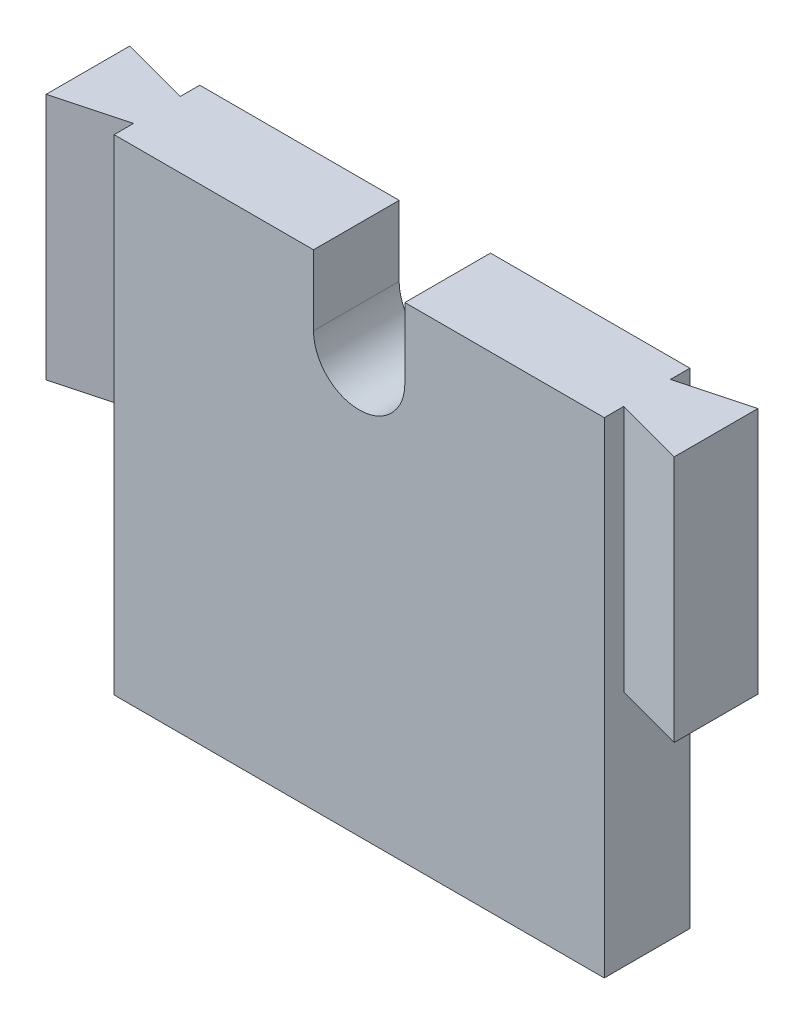
SolidWorks part; units mm, degrees
ref_plane "Front Plane" through (0, 0, 0) normal (0, 0, 1) x (1, 0, 0)
ref_plane "Top Plane" through (0, 0, 0) normal (0, 1, 0) x (1, 0, 0)
ref_plane "Right Plane" through (0, 0, 0) normal (1, 0, 0) x (0, 0, -1)
sketch "Sketch2" plane through (0, 0, 0) normal (0, 0, 1) x (1, 0, 0)
  line L0 (-10.1529, 26.4118) -> (-0.5529, 26.4118)
  line L1 (-38.3529, 26.4118) -> (27.6471, 26.4118)
  line L2 (-38.3529, 26.4118) -> (-38.3529, -24.5882)
  line L3 (-38.3529, -24.5882) -> (27.6471, -24.5882)
  line L4 (27.6471, 26.4118) -> (27.6471, -24.5882)
  line L5 (-5.3529, 26.4118) -> (-5.3529, -24.5882) construction
  line L6 (-10.1529, 19.0368) -> (-10.1529, 26.4118)
  line L7 (-0.5529, 19.0368) -> (-0.5529, 26.4118)
  arc A0 (-10.1529, 19.0368) -> (-0.5529, 19.0368) centre (-5.3529, 19.0368) ccw
  dimension "D4" = 9.6
  dimension "D1" = 66
  dimension "D2" = 51
extrude "Boss-Extrude1" add sketch "Sketch2" along normal blind 9
sketch "Sketch3" plane through (0, 26.4118, 0) normal (0, 1, 0) x (1, 0, 0)
  line L0 (28.0533, 0) -> (20.4026, -2.05)
  line L1 (20.4026, -2.05) -> (20.4026, 0)
  line L2 (-0.5529, 0) -> (27.6471, 0) construction
  line L3 (28.0533, -9) -> (20.4026, -6.95)
  line L4 (20.4026, -6.95) -> (20.4026, -9)
  line L5 (-0.5529, -9) -> (27.6471, -9) construction
  line L6 (27.6471, -9) -> (27.6471, 0) construction
  line L7 (20.4026, 0) -> (28.0533, 0)
  line L8 (28.0533, -9) -> (20.4026, -9)
  line L9 (-38.7592, 0) -> (-31.1085, -2.05)
  line L10 (-38.7592, -9) -> (-31.1085, -6.95)
  line L11 (-31.1085, -6.95) -> (-31.1085, -9)
  line L13 (-31.1085, -2.05) -> (-31.1085, 0)
  line L15 (-38.3529, -9) -> (-38.3529, 0) construction
  line L16 (-38.7592, 0) -> (-31.1085, 0)
  line L17 (-31.1085, -9) -> (-38.7592, -9)
  line L18 (-38.3529, 0) -> (-10.1529, 0) construction
  line L19 (-38.3529, -9) -> (-10.1529, -9) construction
  point P2 (0, 0)
  point P8 (0, 0)
  point P22 (0, 0)
  point P25 (0, 0)
  dimension "D3" = 75
  dimension "D4" = 75
  dimension "D5" = 4.9
  dimension "D8" = 75
  dimension "D9" = 75
extrude "Cut-Extrude1" cut sketch "Sketch3" against normal through all
sketch "Sketch4" plane through (0, -24.5882, 0) normal (0, -1, 0) x (1, 0, 0)
  line L1 (-31.1085, 0) -> (-38.6543, 0)
  line L2 (-31.1085, 0) -> (-31.1085, 9.2028)
  line L3 (-31.1085, 9.2028) -> (-38.6543, 9.2028)
  line L4 (-38.6543, 0) -> (-38.6543, 9.2028)
  line L5 (20.4026, 0) -> (28.5375, 0)
  line L6 (20.4026, 0) -> (20.4026, 9.2028)
  line L7 (20.4026, 9.2028) -> (28.5375, 9.2028)
  line L8 (28.5375, 0) -> (28.5375, 9.2028)
extrude "Cut-Extrude2" cut sketch "Sketch4" against normal blind 25
